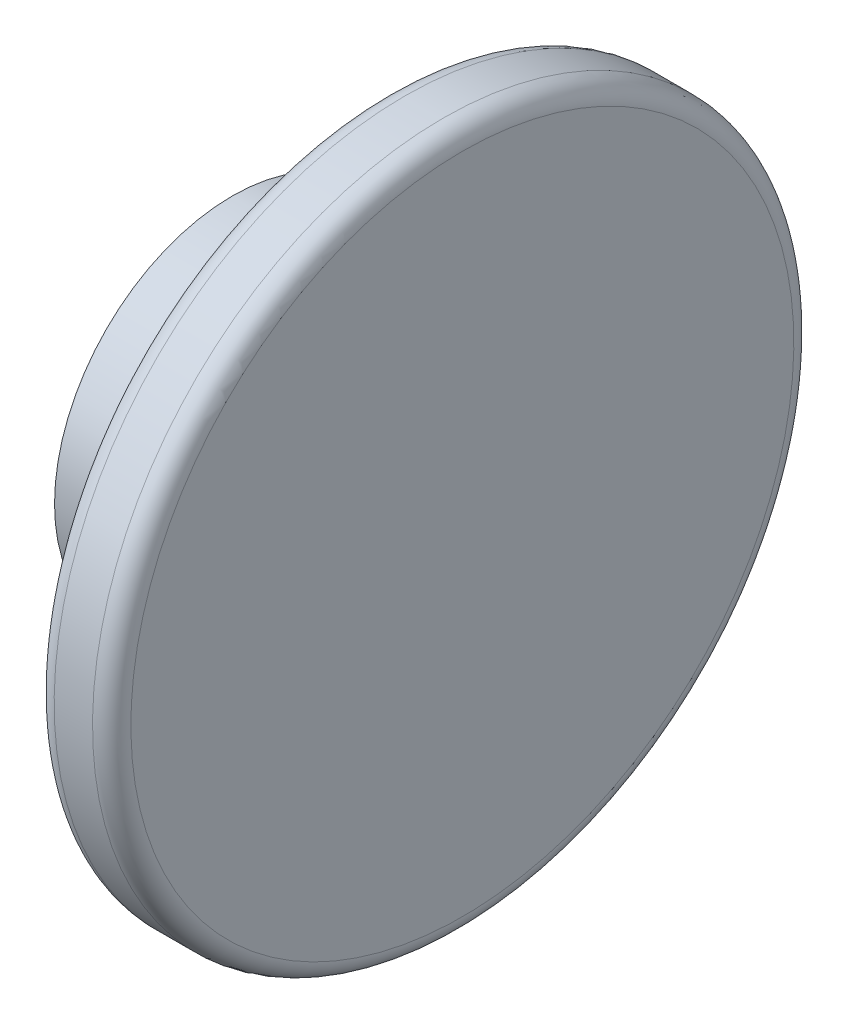
SolidWorks part; units mm, degrees
material "Nylon 6/10"
ref_plane "Front Plane" through (0, 0, 0) normal (0, 0, 1) x (1, 0, 0)
ref_plane "Top Plane" through (0, 0, 0) normal (0, 1, 0) x (1, 0, 0)
ref_plane "Right Plane" through (0, 0, 0) normal (1, 0, 0) x (0, 0, -1)
sketch "Sketch1" plane through (0, 0, 0) normal (0, 0, 1) x (1, 0, 0)
  line L0 (8.255, 0) -> (-8.255, 0) construction
  line L1 (26.25, 0) -> (-26.25, 0) construction
  line L2 (8.255, 0) -> (8.255, 18.542)
  line L3 (8.255, 18.542) -> (26.25, 18.542)
  line L4 (26.25, 18.542) -> (26.25, 0)
  line L5 (8.255, 0) -> (26.25, 0)
  point P4 (0, 0)
  point P8 (0, 0)
  dimension "D1" = 16.51
  dimension "D2" = 52.5
  dimension "D3" = 18.542
revolve "Revolve1" add sketch "Sketch1" angle 360 about L5
sketch "Sketch2" plane through (8.255, 0, 0) normal (-1, 0, 0) x (0, 0, 1)
  circle A0 centre (0, 0) radius 3.7147
  dimension "D1" = 7.4295
extrude "Cut-Extrude1" cut sketch "Sketch2" against normal blind 8.5725 draft 3
sketch "Sketch3" plane through (26.25, 0, 0) normal (1, 0, 0) x (0, 0, -1)
  line L1 (38.1, -54.7688) -> (-38.1, -54.7688) construction
  line L2 (38.1, -54.7688) -> (38.1, 54.7687) construction
  line L3 (38.1, 54.7687) -> (-38.1, 54.7687) construction
  line L4 (-38.1, -54.7688) -> (-38.1, 54.7687) construction
  line L5 (38.1, -54.7688) -> (-38.1, 54.7687) construction
  line L6 (38.1, 54.7687) -> (-38.1, -54.7688) construction
  circle A3 centre (0, 0) radius 36.576
  point P0 (0, 0)
  point P6 (0, 0)
  dimension "D3" = 73.152
  dimension "D1" = 109.5375
  dimension "D2" = 76.2
extrude "Boss-Extrude1" add sketch "Sketch3" along normal blind 8
fillet "Fillet1" radius 2 3 edges at (26.25, 36.576, 0) (34.25, 36.576, 0) (26.25, -18.542, 0)
sketch "Sketch4" plane through (8.255, 0, 0) normal (-1, 0, 0) x (0, 0, 1)
  circle A0 centre (0, 0) radius 18.542 construction
  circle A1 centre (0, 0) radius 18.542
  circle A2 centre (0, 0) radius 12.7
  dimension "D1" = 25.4
extrude "Cut-Extrude2" cut sketch "Sketch4" against normal blind 2
sketch "Sketch5" plane through (0, 0, 0) normal (0, 1, 0) x (1, 0, 0)
  line L0 (8.255, -12.7) -> (10.255, -18.542)
  line L1 (10.255, 18.542) -> (10.255, -18.542) construction
  line L2 (10.255, -18.542) -> (24.25, -18.542) construction
  line L3 (10.255, -18.542) -> (10.255, -12.7)
  line L4 (10.255, -12.7) -> (8.255, -12.7)
  line L5 (0, 0) -> (10.255, 0) construction
  line L6 (10.255, 12.7) -> (10.255, -12.7) construction
revolve "Revolve2" add sketch "Sketch5" angle 360 about L5
fillet "Fillet2" radius 5 1 edges at (8.255, 0, 12.7)
